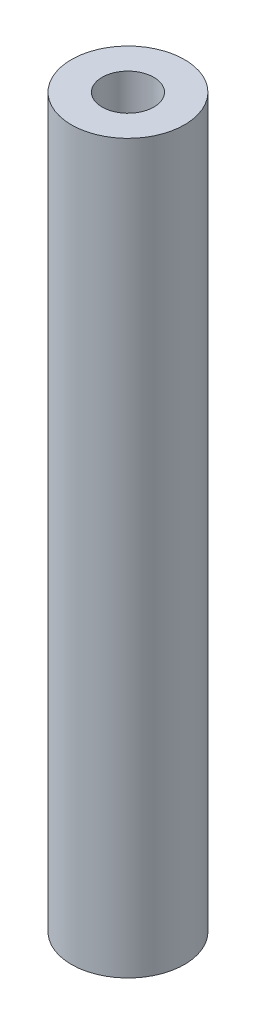
SolidWorks part; units mm, degrees
ref_plane "Front Plane" through (0, 0, 0) normal (0, 0, 1) x (1, 0, 0)
ref_plane "Top Plane" through (0, 0, 0) normal (0, 1, 0) x (1, 0, 0)
ref_plane "Right Plane" through (0, 0, 0) normal (1, 0, 0) x (0, 0, -1)
sketch "Sketch1" plane through (0, 0, 0) normal (0, 1, 0) x (1, 0, 0)
  circle A0 centre (0, 0) radius 7
  circle A1 centre (0, 0) radius 3.2
  dimension "D1" = 6.4
  dimension "D2" = 14
extrude "Boss-Extrude1" add sketch "Sketch1" along normal blind 90
